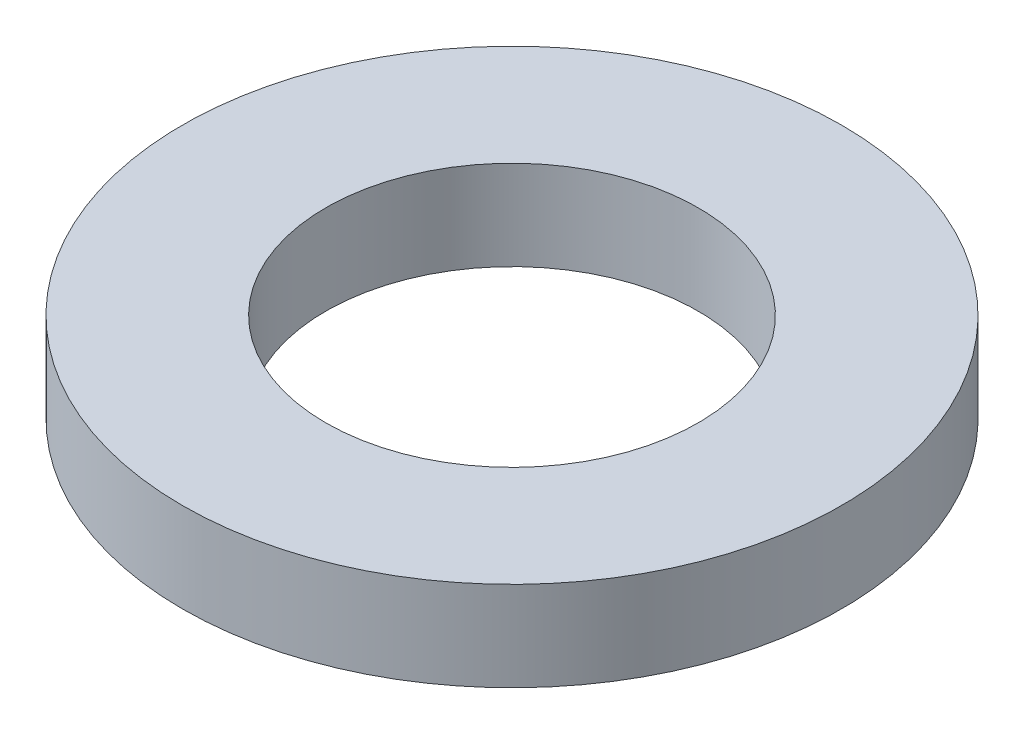
SolidWorks part; units mm, degrees
material "Nylon 101"
ref_plane "Front Plane" through (0, 0, 0) normal (0, 0, 1) x (1, 0, 0)
ref_plane "Top Plane" through (0, 0, 0) normal (0, 1, 0) x (1, 0, 0)
ref_plane "Right Plane" through (0, 0, 0) normal (1, 0, 0) x (0, 0, -1)
sketch "Sketch1" plane through (0, 0, 0) normal (0, 1, 0) x (1, 0, 0)
  circle A0 centre (0, 0) radius 5.842
  circle A1 centre (0, 0) radius 3.302
  dimension "D1" = 6.604
  dimension "D2" = 11.684
extrude "Boss-Extrude1" add sketch "Sketch1" along normal blind 1.5875
